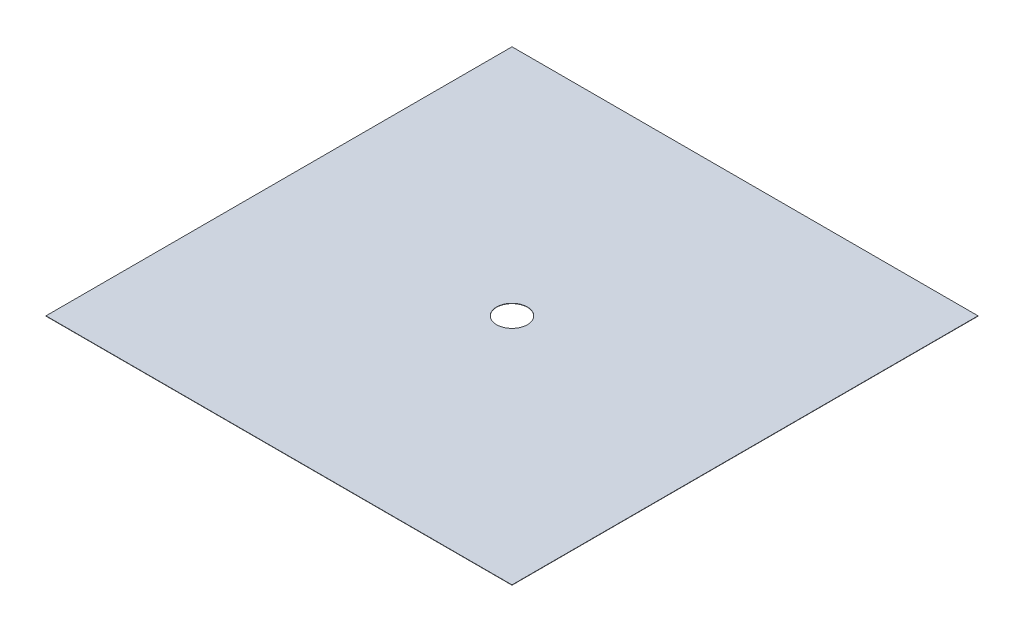
SolidWorks part; units mm, degrees
ref_plane "Front Plane" through (0, 0, 0) normal (0, 0, 1) x (1, 0, 0)
ref_plane "Top Plane" through (0, 0, 0) normal (0, 1, 0) x (1, 0, 0)
ref_plane "Right Plane" through (0, 0, 0) normal (1, 0, 0) x (0, 0, -1)
sketch "Sketch1" plane through (0, 0, 0) normal (0, 1, 0) x (1, 0, 0)
  line L0 (0, 0) -> (-530, 0)
  line L1 (-530, 0) -> (-530, 530)
  line L2 (-530, 530) -> (0, 530)
  line L3 (0, 530) -> (0, 0)
  line L4 (-265, 0) -> (-265, 530) construction
  line L6 (-530, 265) -> (0, 265) construction
  circle A0 centre (-265, 265) radius 17.5
  point P7 (0, 0)
  point P12 (-265, 265)
  dimension "D3" = 35
  dimension "D1" = 530
  dimension "D2" = 530
extrude "Boss-Extrude1" add sketch "Sketch1" along normal blind 0.35
